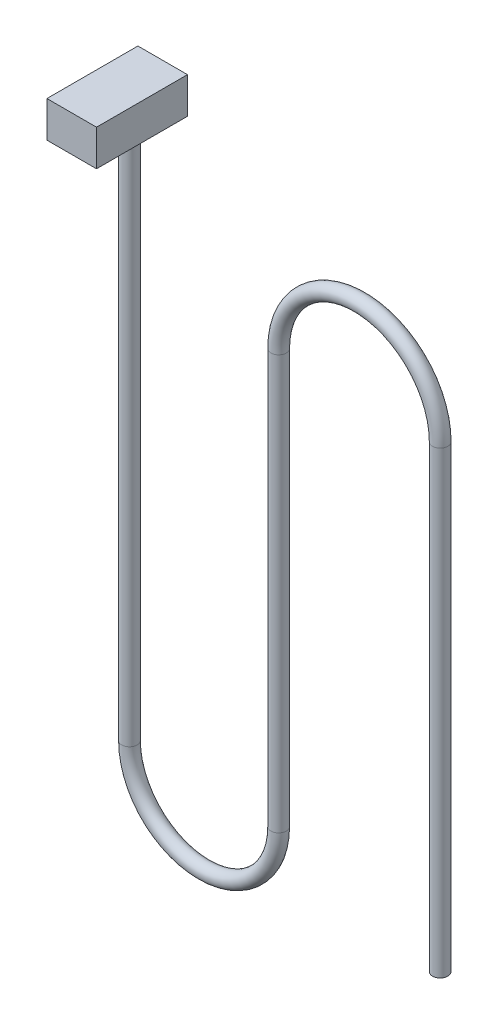
SolidWorks part; units mm, degrees
ref_plane "Front Plane" through (0, 0, 0) normal (0, 0, 1) x (1, 0, 0)
ref_plane "Top Plane" through (0, 0, 0) normal (0, 1, 0) x (1, 0, 0)
ref_plane "Right Plane" through (0, 0, 0) normal (1, 0, 0) x (0, 0, -1)
sketch "Sketch1" plane through (0, 0, 0) normal (0, 0, 1) x (1, 0, 0)
  line L1 (-47.2308, 74.3308) -> (-55.4082, 74.3308)
  line L2 (-47.2308, 74.3308) -> (-47.2308, 68.384)
  line L3 (-47.2308, 68.384) -> (-55.4082, 68.384)
  line L4 (-55.4082, 74.3308) -> (-55.4082, 68.384)
extrude "Boss-Extrude1" add sketch "Sketch1" against normal blind 15
sketch "Sketch2" plane through (0, 68.384, 0) normal (0, -1, 0) x (1, 0, 0)
  line L0 (-51.3195, 0) -> (-51.3195, -9.5228) construction
  line L1 (-55.4082, 0) -> (-47.2308, 0) construction
  circle A0 centre (-51.3195, -9.5228) radius 1.27
  dimension "D1" = 2.54
ref_plane "Plane1" through (0, 0, -9.5228) normal (0, 0, 1) x (1, 0, 0)
sketch "Sketch3" plane through (0, 0, -9.5228) normal (0, 0, 1) x (1, 0, 0)
  line L0 (-51.3195, 68.384) -> (-51.3195, -20.049)
  line L1 (-52.5895, 68.384) -> (-50.0495, 68.384) construction
  line L2 (-26.7268, -20.049) -> (-26.7268, 48.2105)
  line L3 (-0.0913, 48.2105) -> (-0.0913, -27.4446)
  arc A0 (-51.3195, -20.049) -> (-26.7268, -20.049) centre (-39.0232, -20.049) ccw
  arc A1 (-26.7268, 48.2105) -> (-0.0913, 48.2105) centre (-13.4091, 48.2105) cw
sweep "Sweep1" add profiles "Sketch2" path "Sketch3"
